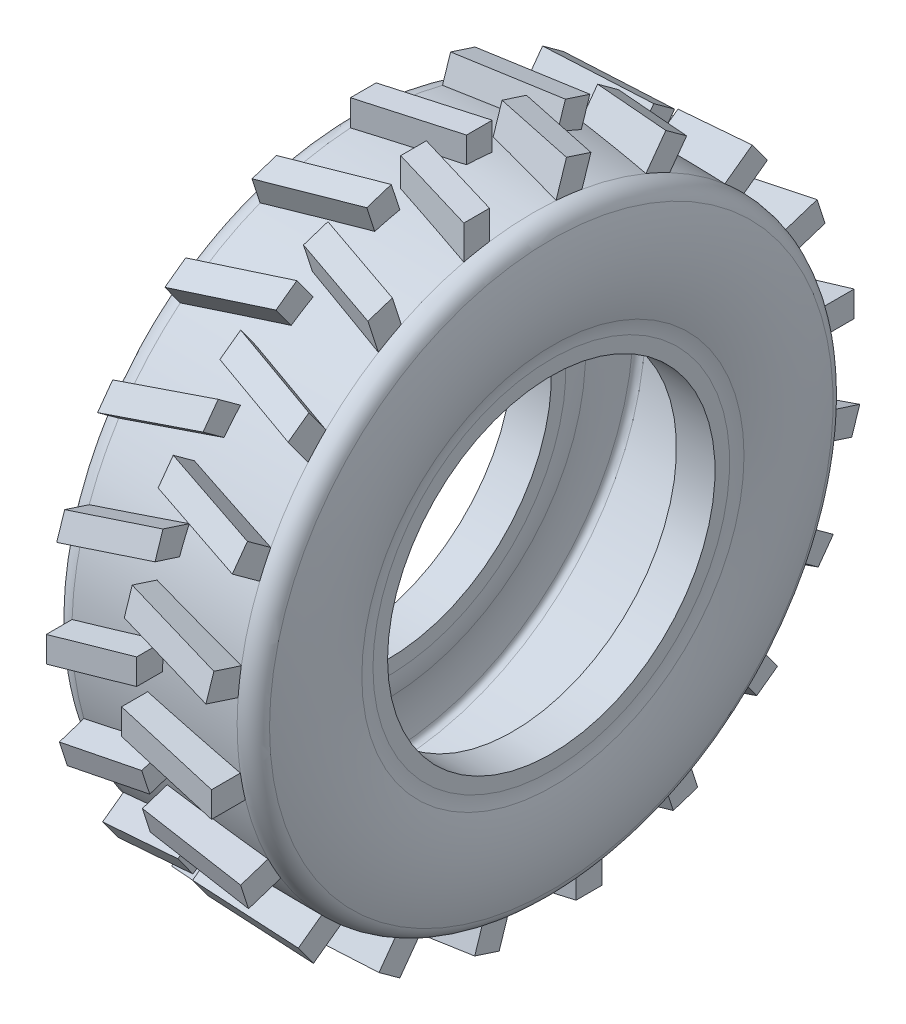
SolidWorks part; units mm, degrees
ref_plane "Front Plane" through (0, 0, 0) normal (0, 0, 1) x (1, 0, 0)
ref_plane "Top Plane" through (0, 0, 0) normal (0, 1, 0) x (1, 0, 0)
ref_plane "Right Plane" through (0, 0, 0) normal (1, 0, 0) x (0, 0, -1)
sketch "Sketch1" plane through (0, 0, 0) normal (0, 0, 1) x (1, 0, 0)
  line L0 (0, 71.4858) -> (0, -64.2704) construction
  line L1 (-86.8519, 0) -> (93.5328, 0) construction
  line L2 (0, 40.0047) -> (-10.4892, 40.0047) construction
  line L3 (0, 46.0047) -> (12.8573, 46.0047)
  line L4 (15.7323, 27.7533) -> (15.7323, 25.4808)
  line L5 (2.2929, 40.0047) -> (2.2929, 40.0047)
  line L6 (2.2929, 40.0047) -> (9.6356, 40.0047)
  line L7 (9.7323, 27.7533) -> (9.7323, 25.4808)
  line L8 (15.7323, 25.4808) -> (9.7323, 25.4808)
  line L9 (0, 40.0047) -> (2.2929, 40.0047)
  line L10 (-15.7323, 27.7533) -> (-15.7323, 25.4808)
  line L11 (0, 46.0047) -> (-12.8573, 46.0047)
  line L12 (0, 40.0047) -> (-9.6356, 40.0047)
  line L13 (-9.7323, 27.7533) -> (-9.7323, 25.4808)
  line L14 (-15.7323, 25.4808) -> (-9.7323, 25.4808)
  line L15 (0, 45.5493) -> (0, 46.0047) construction
  line L16 (2.2929, 40.0047) -> (10.4892, 40.0047) construction
  arc A0 (15.7352, 43.8519) -> (15.9832, 29.7412) centre (-9.7626, 36.3462) cw
  arc A1 (15.9832, 29.7412) -> (15.7323, 27.7533) centre (23.7323, 27.7533) ccw
  arc A3 (12.8573, 46.0047) -> (15.7352, 43.8519) centre (12.8573, 43.0047) cw
  arc A4 (10.6264, 39.1405) -> (10.1714, 31.2322) centre (-9.7626, 36.3462) cw
  arc A5 (10.1714, 31.2322) -> (9.7323, 27.7533) centre (23.7323, 27.7533) ccw
  arc A6 (-15.9832, 29.7412) -> (-15.7323, 27.7533) centre (-23.7323, 27.7533) cw
  arc A7 (-15.7352, 43.8519) -> (-15.9832, 29.7412) centre (9.7626, 36.3462) ccw
  arc A8 (-12.8573, 46.0047) -> (-15.7352, 43.8519) centre (-12.8573, 43.0047) ccw
  arc A9 (10.4892, 40.0047) -> (10.1714, 31.2322) centre (-9.7626, 36.3462) cw construction
  arc A10 (-10.6264, 39.1405) -> (-10.1714, 31.2322) centre (9.7626, 36.3462) ccw
  arc A11 (-10.1714, 31.2322) -> (-9.7323, 27.7533) centre (-23.7323, 27.7533) cw
  arc A12 (-10.4892, 40.0047) -> (-10.1714, 31.2322) centre (9.7626, 36.3462) ccw construction
  arc A13 (-10.6264, 39.1405) -> (-9.6356, 40.0047) centre (-9.6356, 39.0047) cw
  arc A14 (-10.4892, 40.0047) -> (-10.4892, 40.0047) centre (-10.4892, 40.0047) ccw construction
  arc A15 (10.6264, 39.1405) -> (9.6356, 40.0047) centre (9.6356, 39.0047) ccw
  arc A16 (10.4892, 40.0047) -> (10.4892, 40.0047) centre (10.4892, 40.0047) cw construction
  point P17 (15, 46.0047)
  dimension "D1" = 8
  dimension "D5" = 3
  dimension "D8" = 1
  dimension "D9" = 1
  dimension "D2" = 15
  dimension "D6" = 6
  dimension "D7" = 6
revolve "Revolve1" add sketch "Sketch1" angle 360 about L1
ref_plane "Plane1" through (0, 50, 0) normal (0, 1, 0) x (1, 0, 0)
sketch "Sketch2" plane through (0, 50, 0) normal (0, 1, 0) x (1, 0, 0)
  line L0 (0, 25.5412) -> (0, -28.528) construction
  line L1 (-1.1421, -2.5621) -> (-1.1421, -6.5621)
  line L2 (-1.1421, -6.5621) -> (12.8573, -10.7394)
  line L3 (12.8573, -46.0047) -> (12.8573, 46.0047) construction
  line L4 (12.8573, -10.7394) -> (12.8573, -6.7394)
  line L5 (12.8573, -6.7394) -> (-1.1421, -2.5621)
  line L6 (1.2077, 1.3356) -> (1.2077, 5.3356)
  line L7 (1.2077, 5.3356) -> (-12.8573, 1.3356)
  line L8 (-12.8573, -46.0047) -> (-12.8573, 46.0047) construction
  line L9 (-12.8573, 1.3356) -> (-12.8573, -2.6644)
  line L10 (-12.8573, -2.6644) -> (1.2077, 1.3356)
  dimension "D1" = 4
  dimension "D2" = 4
  dimension "D3" = 4
  dimension "D4" = 4
extrude "Boss-Extrude1" add sketch "Sketch2" against normal up to next
pattern_circular "CirPattern1" count 20 over 360 about axis through (0, 0, 0) along (1, 0, 0) of "Boss-Extrude1"
